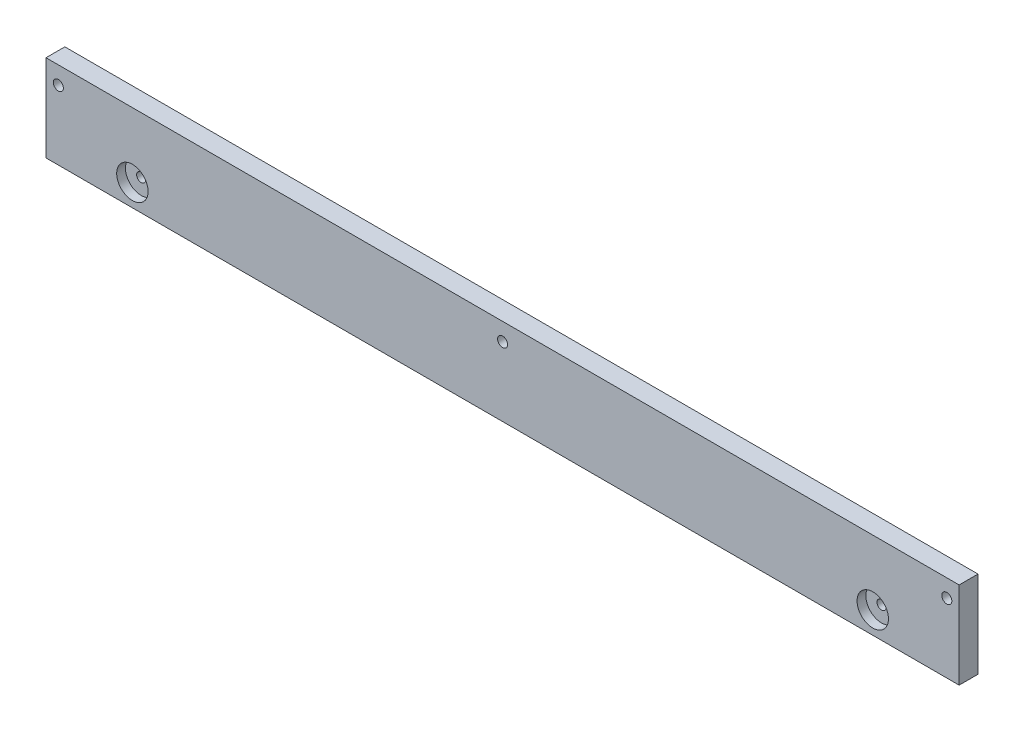
SolidWorks part; units mm, degrees
ref_plane "Plane1" through (0, 0, 0) normal (0, 0, 1) x (1, 0, 0)
ref_plane "Plane2" through (0, 0, 0) normal (0, 1, 0) x (1, 0, 0)
ref_plane "Plane3" through (0, 0, 0) normal (1, 0, 0) x (0, 0, -1)
sketch "Esquisse5" plane through (0, 0, 0) normal (0, 0, 1) x (1, 0, 0)
  line L0 (-15.1521, 0) -> (293.7692, 0) construction
  line L1 (286.6703, -7.5066) -> (286.6703, 40.9084) construction
  line L2 (293.7692, 27.625) -> (-15.1521, 27.625) construction
  line L3 (-3.927, 38.1576) -> (-3.927, -7.5066) construction
  line L5 (-3.927, 27.625) -> (286.6703, 27.625)
  line L6 (-3.927, 27.625) -> (-3.927, 0)
  line L7 (-3.927, 0) -> (286.6703, 0)
  line L8 (286.6703, 27.625) -> (286.6703, 0)
  circle A0 centre (282.7433, 22) radius 1.6
  circle A2 centre (0, 22) radius 1.6
  circle A3 centre (141.3732, 22) radius 1.6
extrude "Extrusion1" add sketch "Esquisse5" along normal blind 6
sketch "Esquisse4" plane through (0, 0, 6) normal (0, 0, 1) x (1, 0, 0)
  circle A0 centre (23.5619, 7) radius 5
  circle A2 centre (259.1814, 7) radius 5
extrude "Enlèv. mat.-Extru.2" cut sketch "Esquisse4" against normal blind 2.8
sketch "Esquisse6" plane through (0, 0, 3.2) normal (0, 0, 1) x (1, 0, 0)
  circle A0 centre (23.5619, 7) radius 1.45
  circle A1 centre (259.1814, 7) radius 1.45
extrude "Enlèv. mat.-Extru.3" cut sketch "Esquisse6" against normal blind 2.5
